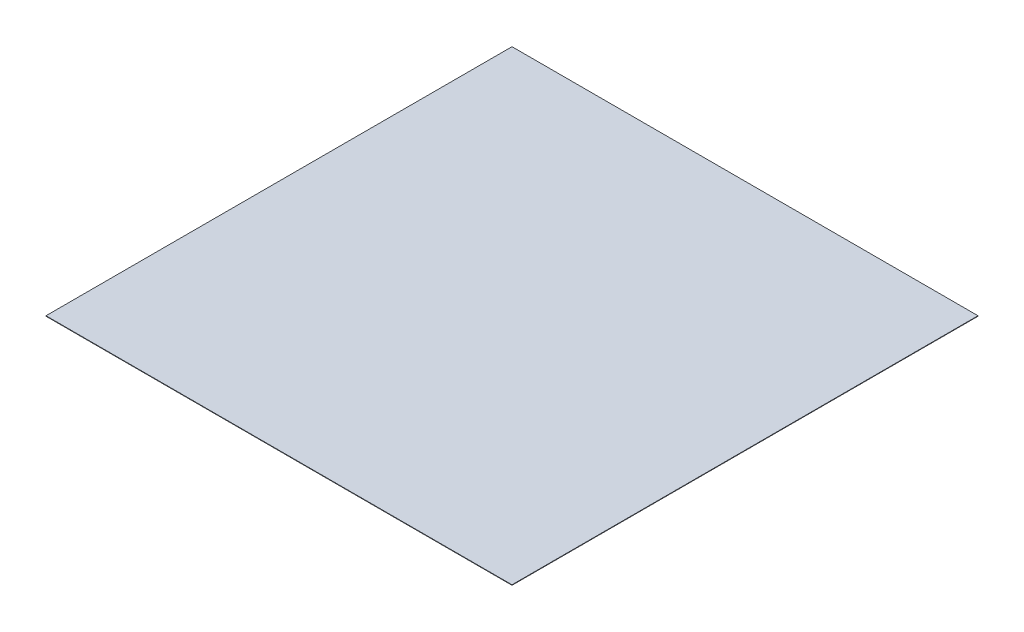
SolidWorks part; units mm, degrees
ref_plane "前视基准面" through (0, 0, 0) normal (0, 0, 1) x (1, 0, 0)
ref_plane "上视基准面" through (0, 0, 0) normal (0, 1, 0) x (1, 0, 0)
ref_plane "右视基准面" through (0, 0, 0) normal (1, 0, 0) x (0, 0, -1)
sketch "草图1" plane through (0, 0, 0) normal (0, 1, 0) x (1, 0, 0)
  line L1 (-500, -500) -> (500, -500)
  line L2 (-500, -500) -> (-500, 500)
  line L3 (-500, 500) -> (500, 500)
  line L4 (500, -500) -> (500, 500)
  line L5 (-500, -500) -> (500, 500) construction
  line L6 (-500, 500) -> (500, -500) construction
  point P0 (0, 0)
  dimension "D1" = 1000
  dimension "D2" = 1000
extrude "凸台-拉伸1" add sketch "草图1" along normal blind 1
